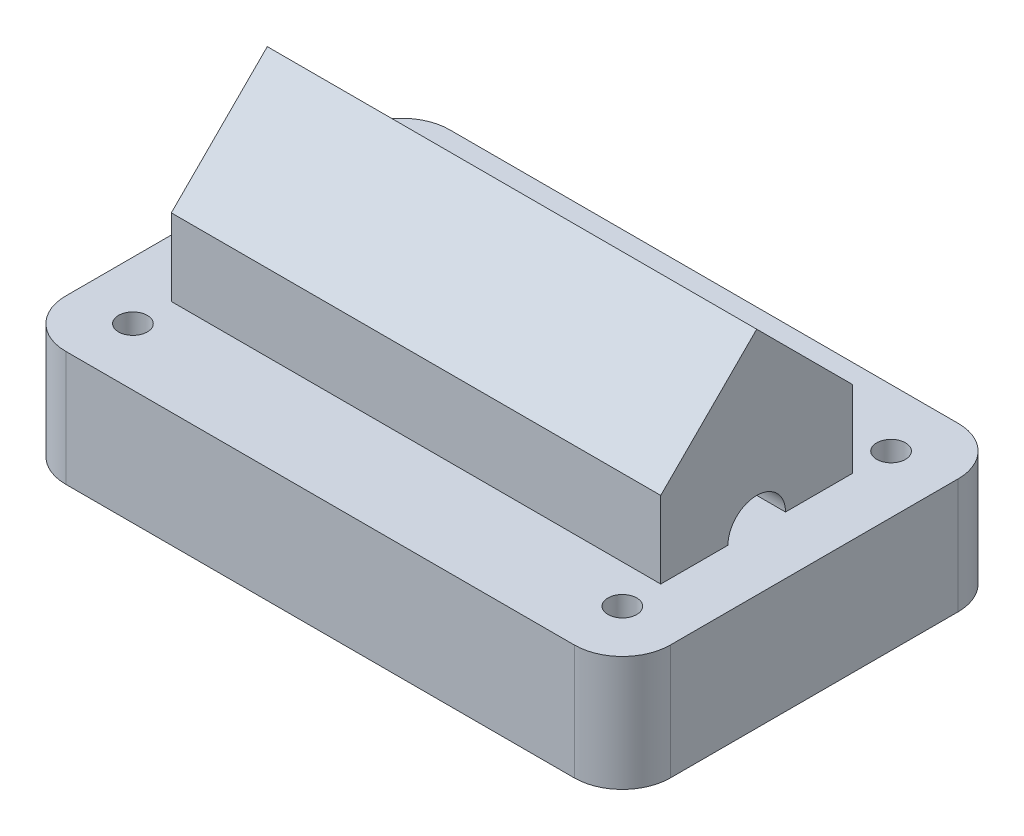
SolidWorks part; units mm, degrees
ref_plane "Ön Düzlem" through (0, 0, 0) normal (0, 0, 1) x (1, 0, 0)
ref_plane "Üst Düzlem" through (0, 0, 0) normal (0, 1, 0) x (1, 0, 0)
ref_plane "Sağ Düzlem" through (0, 0, 0) normal (1, 0, 0) x (0, 0, -1)
sketch "Çizim1" plane through (0, 0, 0) normal (0, 1, 0) x (1, 0, 0)
  line L1 (-157.5, 100) -> (157.5, 100)
  line L2 (-157.5, 100) -> (-157.5, -100)
  line L3 (-157.5, -100) -> (157.5, -100)
  line L4 (157.5, 100) -> (157.5, -100)
  line L5 (-157.5, 100) -> (157.5, -100) construction
  line L6 (-157.5, -100) -> (157.5, 100) construction
  point P0 (0, 0)
  dimension "D1" = 200
  dimension "D2" = 315
extrude "Yükseklik-Ekstrüzyon1" add sketch "Çizim1" along normal blind 60
fillet "Radyus1" radius 25 4 edges at (-157.5, 30, -100) (-157.5, 30, 100) (157.5, 30, -100) (157.5, 30, 100)
sketch "Çizim2" plane through (0, 60, 0) normal (0, 1, 0) x (1, 0, 0)
  line L0 (132.5, 100) -> (-132.5, 100) construction
  line L1 (-157.5, 75) -> (-157.5, -75) construction
  line L2 (0, 0) -> (0, 55.3395) construction
  line L3 (0, 0) -> (46.5015, 0) construction
  circle A0 centre (-127.5, 70) radius 7.5
  circle A1 centre (127.5, 70) radius 7.5
  circle A2 centre (127.5, -70) radius 7.5
  circle A3 centre (-127.5, -70) radius 7.5
  dimension "D3" = 15
  dimension "D1" = 30
  dimension "D2" = 30
extrude "Kes-Ekstrüzyon1" cut sketch "Çizim2" against normal through all
sketch "Çizim3" plane through (0, 60, 0) normal (0, 1, 0) x (1, 0, 0)
  line L0 (-157.5, 75) -> (-157.5, -75) construction
  line L1 (127.5, 50) -> (-127.5, 50)
  line L2 (127.5, 50) -> (127.5, -50)
  line L3 (127.5, -50) -> (-127.5, -50)
  line L4 (-127.5, 50) -> (-127.5, -50)
  line L5 (127.5, 50) -> (-127.5, -50) construction
  line L6 (127.5, -50) -> (-127.5, 50) construction
  point P0 (0, 0)
  point P6 (-120.8342, -48.8548)
  point P7 (0, 0)
  point P10 (-117.5, 48.8212)
  point P11 (0, 0)
  point P12 (-117.5, -56.621)
  dimension "D1" = 30
  dimension "D2" = 100
extrude "Yükseklik-Ekstrüzyon2" add sketch "Çizim3" along normal blind 40
sketch "Çizim4" plane through (127.5, 0, 0) normal (1, 0, 0) x (0, 0, -1)
  line L0 (-50, 100) -> (0, 150)
  line L1 (0, 150) -> (50, 100)
  line L2 (50, 100) -> (-50, 100)
  point P3 (0, 0)
  dimension "D1" = 90
extrude "Yükseklik-Ekstrüzyon3" add sketch "Çizim4" against normal up to surface (255 mm away) up to face at (-127.5, 80, 0)
sketch "Çizim5" plane through (127.5, 0, 0) normal (1, 0, 0) x (0, 0, -1)
  line L0 (-50, 60) -> (50, 60) construction
  line L1 (-15, 60) -> (15, 60)
  arc A0 (15, 60) -> (-15, 60) centre (0, 60) ccw
  dimension "D1" = 30
extrude "Kes-Ekstrüzyon2" cut sketch "Çizim5" against normal through all
